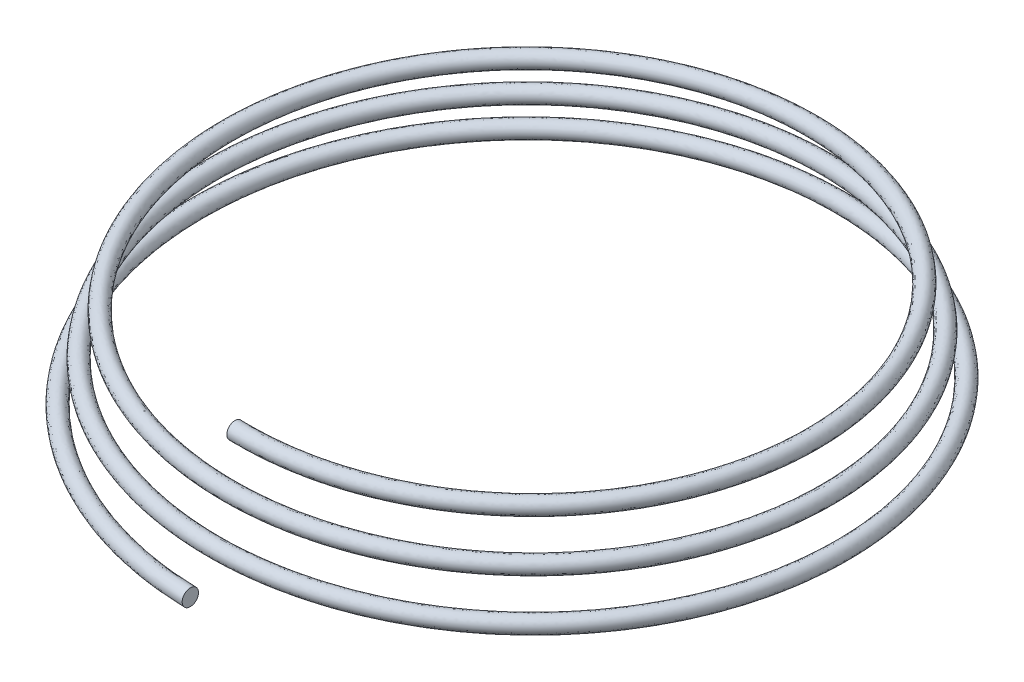
SolidWorks part; units mm, degrees
ref_plane "前视基准面" through (0, 0, 0) normal (0, 0, 1) x (1, 0, 0)
ref_plane "上视基准面" through (0, 0, 0) normal (0, 1, 0) x (1, 0, 0)
ref_plane "右视基准面" through (0, 0, 0) normal (1, 0, 0) x (0, 0, -1)
sketch "草图1" plane through (0, 0, 0) normal (0, 1, 0) x (1, 0, 0)
  circle A0 centre (0, 0) radius 4
  dimension "D1" = 8
curve "螺旋线/涡状线1"
sketch "草图3" plane through (0, 0, 0) normal (1, 0, 0) x (0, 0, -1)
  circle A0 centre (-4, 0) radius 0.1
  dimension "D1" = 0.2
  dimension "D2" = 4
sweep "扫描1" add profiles "草图3" path "螺旋线/涡状线1"
sketch "草图4" plane through (0, 0, 0) normal (0, 0, 1) x (1, 0, 0)
  line L0 (0, 0) -> (0, 7.4155) construction
equation "\"0。2\"=0.461373"
